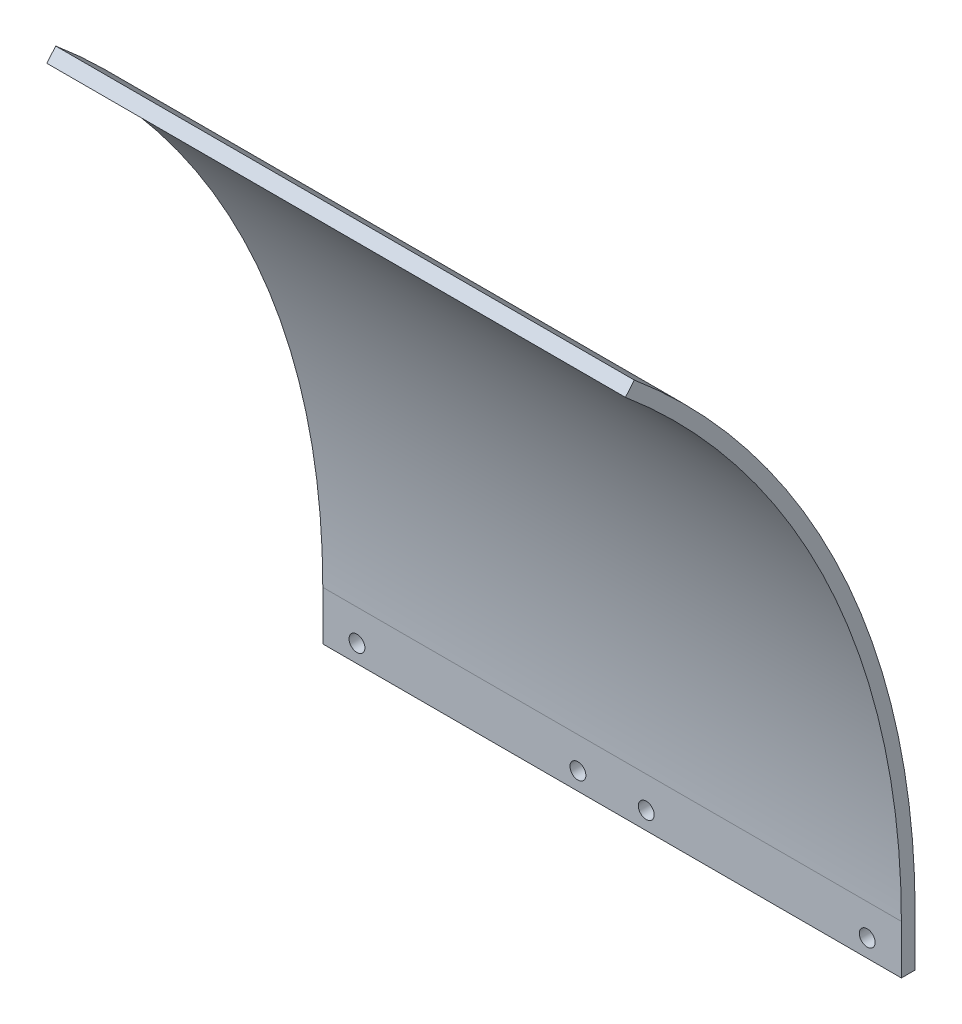
SolidWorks part; units mm, degrees
ref_plane "Front" through (0, 0, 0) normal (0, 0, 1) x (1, 0, 0)
ref_plane "Top" through (0, 0, 0) normal (0, 1, 0) x (1, 0, 0)
ref_plane "Right" through (0, 0, 0) normal (1, 0, 0) x (0, 0, -1)
sketch "Sketch1" plane through (0, 0, 0) normal (1, 0, 0) x (0, 0, -1)
  line L0 (0, 178.054) -> (0, 181.229)
  line L1 (178.054, 0) -> (181.229, 0)
  arc A0 (178.054, 0) -> (0, 178.054) centre (0, 0) ccw
  arc A1 (181.229, 0) -> (0, 181.229) centre (0, 0) ccw
  dimension "D1" = 356.108
  dimension "D2" = 3.175
extrude "Boss-Extrude1" add sketch "Sketch1" along normal blind 133.35
sketch "Sketch2" plane through (133.35, 0, 0) normal (1, 0, 0) x (0, 0, -1)
  line L0 (0, 0) -> (178.054, 0) construction
  line L1 (0, 0) -> (114.4509, 136.3973) construction
  line L2 (114.4509, 136.3973) -> (116.4918, 138.8295)
  line L3 (0, 178.054) -> (0, 181.229)
  arc A0 (178.054, 0) -> (0, 178.054) centre (0, 0) ccw construction
  arc A2 (0, 178.054) -> (114.4509, 136.3973) centre (0, 0) cw
  arc A3 (0, 181.229) -> (116.4918, 138.8295) centre (0, 0) cw
  dimension "D1" = 50
extrude "Cut-Extrude1" cut sketch "Sketch2" against normal through all
sketch "Sketch3" plane through (0, 0, 0) normal (0, -1, 0) x (1, 0, 0)
  line L1 (0, -181.229) -> (133.35, -181.229)
  line L2 (0, -181.229) -> (0, -178.054)
  line L3 (0, -178.054) -> (133.35, -178.054)
  line L4 (133.35, -181.229) -> (133.35, -178.054)
extrude "Boss-Extrude2" add sketch "Sketch3" along normal blind 11.303
sketch "Sketch4" plane through (0, 0, -178.054) normal (0, 0, 1) x (1, 0, 0)
  line L0 (0, -11.303) -> (7.874, -11.303) construction
  line L1 (133.35, -11.303) -> (0, -11.303) construction
  line L2 (7.874, -11.303) -> (7.874, -7.239) construction
  line L3 (66.675, -11.303) -> (66.675, 136.3973) construction
  line L4 (0, 136.3973) -> (133.35, 136.3973) construction
  line L5 (66.675, -11.303) -> (58.801, -11.303) construction
  line L6 (58.801, -11.303) -> (58.801, -7.239) construction
  circle A0 centre (7.874, -7.239) radius 1.8288
  circle A1 centre (58.801, -7.239) radius 1.8288
  circle A2 centre (74.549, -7.239) radius 1.8288
  circle A3 centre (125.476, -7.239) radius 1.8288
  dimension "D1" = 7.874
  dimension "D3" = 3.6576
  dimension "D6" = 3.6576
  dimension "D4" = 7.874
  dimension "D2" = 4.064
  dimension "D5" = 4.064
extrude "Cut-Extrude2" cut sketch "Sketch4" against normal through all
